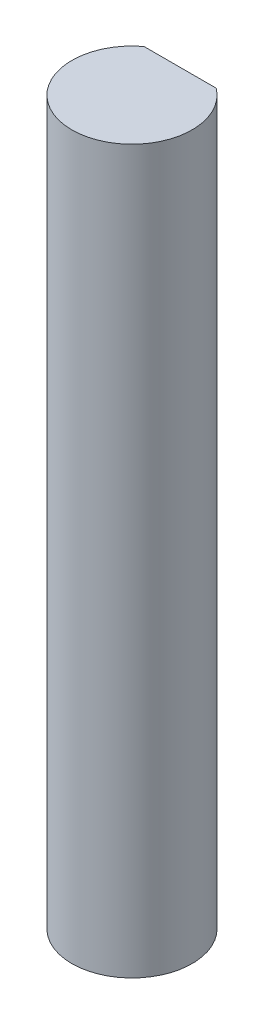
SolidWorks part; units mm, degrees
ref_plane "Front Plane" through (0, 0, 0) normal (0, 0, 1) x (1, 0, 0)
ref_plane "Top Plane" through (0, 0, 0) normal (0, 1, 0) x (1, 0, 0)
ref_plane "Right Plane" through (0, 0, 0) normal (1, 0, 0) x (0, 0, -1)
sketch "Sketch1" plane through (0, 0, 0) normal (0, 1, 0) x (1, 0, 0)
  line L0 (-1.905, 2.54) -> (1.905, 2.54)
  arc A0 (-1.905, 2.54) -> (1.905, 2.54) centre (0, 0) ccw
  dimension "D1" = 6.35
  dimension "D2" = 2.54
extrude "Boss-Extrude1" add sketch "Sketch1" along normal blind 38.1
